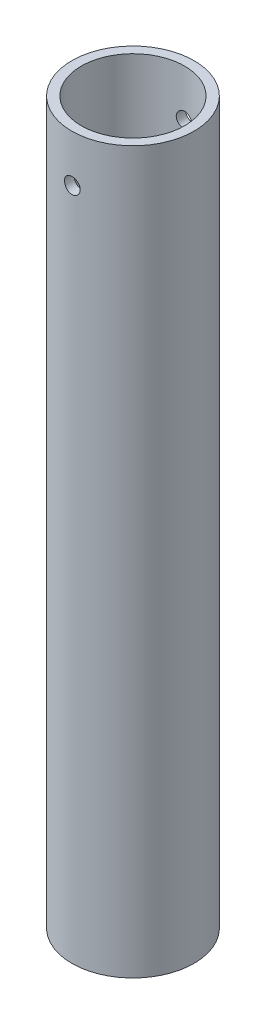
SolidWorks part; units mm, degrees
ref_plane "前视基准面" through (0, 0, 0) normal (0, 0, 1) x (1, 0, 0)
ref_plane "上视基准面" through (0, 0, 0) normal (0, 1, 0) x (1, 0, 0)
ref_plane "右视基准面" through (0, 0, 0) normal (1, 0, 0) x (0, 0, -1)
sketch "草图1" plane through (0, 0, 0) normal (0, 1, 0) x (1, 0, 0)
  circle A0 centre (0, 0) radius 16.5
  circle A1 centre (0, 0) radius 19.5
  dimension "D1" = 39
  dimension "D2" = 3
extrude "凸台-拉伸1" add sketch "草图1" along normal blind 230
sketch "草图2" plane through (0, 0, 0) normal (0, 0, 1) x (1, 0, 0)
  line L0 (16.5, 230) -> (-16.5, 230) construction
  circle A0 centre (0, 215) radius 2.5
  dimension "D1" = 5
  dimension "D2" = 15
extrude "切除-拉伸1" cut sketch "草图2" against normal through all and the other way through all
